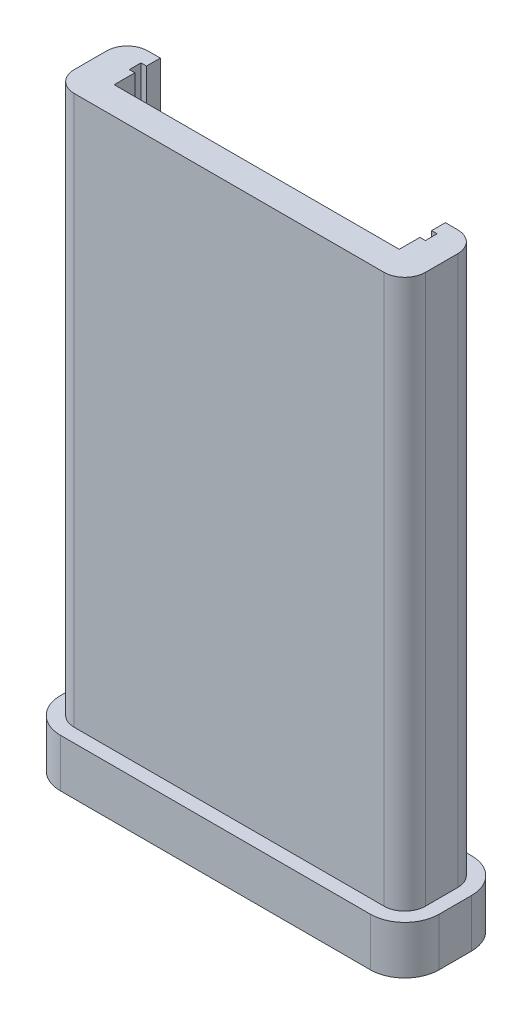
SolidWorks part; units mm, degrees
material "Melamine resin"
ref_plane "Front Plane" through (0, 0, 0) normal (0, 0, 1) x (1, 0, 0)
ref_plane "Top Plane" through (0, 0, 0) normal (0, 1, 0) x (1, 0, 0)
ref_plane "Right Plane" through (0, 0, 0) normal (1, 0, 0) x (0, 0, -1)
sketch "Sketch2" plane through (0, 0, 0) normal (0, 1, 0) x (1, 0, 0)
  line L1 (0, 0) -> (88.9, 0)
  line L2 (0, 0) -> (0, 152.4)
  line L3 (0, 152.4) -> (88.9, 152.4)
  line L10 (88.9, 152.4) -> (88.9, 0)
  dimension "D1" = 152.4
  dimension "D2" = 88.9
extrude "Boss-Extrude1" add sketch "Sketch2" along normal blind 5.9944 contours L3 L10 L1 L2
sketch "Sketch4" plane through (0, 5.9944, 0) normal (0, 1, 0) x (1, 0, 0)
  line L0 (0, 0) -> (0, 152.4) construction
  line L1 (0, 0) -> (88.9, 0) construction
  circle A0 centre (45.72, 109.8713) radius 2.7305
  circle A1 centre (45.72, 33.6713) radius 2.7305
  dimension "D3" = 5.461
  dimension "D4" = 5.461
  dimension "D1" = 76.2
  dimension "D2" = 45.72
  dimension "D5" = 33.6713
extrude "Cut-Extrude2" cut sketch "Sketch4" against normal through all both
sketch "Sketch5" plane through (0, 5.9944, 0) normal (0, 1, 0) x (1, 0, 0)
  line L0 (0, 152.4) -> (88.9, 152.4) construction
  line L1 (12.065, 16.129) -> (76.835, 16.129)
  line L2 (12.065, 16.129) -> (12.065, 2.54)
  line L3 (12.065, 2.54) -> (76.835, 2.54)
  line L4 (76.835, 16.129) -> (76.835, 2.54)
  line L5 (18.161, 7.62) -> (70.739, 7.62)
  line L6 (18.161, 7.62) -> (18.161, 16.129)
  line L7 (18.161, 16.129) -> (70.739, 16.129)
  line L8 (70.739, 7.62) -> (70.739, 16.129)
  line L9 (17.145, 13.589) -> (71.755, 13.589)
  line L10 (17.145, 13.589) -> (17.145, 11.43)
  line L11 (17.145, 11.43) -> (71.755, 11.43)
  line L12 (71.755, 13.589) -> (71.755, 11.43)
  line L13 (0, 0) -> (88.9, 0) construction
  point P16 (44.45, 152.4)
  point P17 (44.45, 16.129)
  dimension "D1" = 54.61
  dimension "D2" = 1.016
  dimension "D3" = 1.016
  dimension "D4" = 3.81
  dimension "D5" = 2.54
  dimension "D6" = 5.08
  dimension "D7" = 5.08
  dimension "D8" = 2.159
  dimension "D9" = 2.54
  dimension "D10" = 5.08
extrude "Boss-Extrude2" add sketch "Sketch5" along normal blind 101.6 contours L9 L12 L11 L8 L5 L6 L10 L1 L2 L3 L4
fillet "Fillet1" radius 3.81 4 edges at (12.065, 56.7944, -2.54) (12.065, 56.7944, -16.129) (76.835, 56.7944, -2.54) (76.835, 56.7944, -16.129)
sketch "Sketch7" plane through (0, 5.9944, 0) normal (0, 1, 0) x (1, 0, 0)
  line L0 (0, 0) -> (88.9, 0) construction
  line L1 (0, 152.4) -> (2.54, 152.4)
  line L2 (0, 152.4) -> (0, 0)
  line L3 (0, 0) -> (2.54, 0)
  line L4 (2.54, 152.4) -> (2.54, 0)
  dimension "D1" = 2.54
extrude "Cut-Extrude3" cut sketch "Sketch7" against normal through all both
sketch "Sketch11" plane through (0, 0, 0) normal (0, -1, 0) x (1, 0, 0)
  line L4 (2.54, 0) -> (2.54, -152.4)
  line L5 (2.54, -152.4) -> (88.9, -152.4)
  line L6 (88.9, -152.4) -> (88.9, 0)
  line L7 (88.9, 0) -> (2.54, 0)
  line L8 (2.54, 0) -> (2.54, -152.4)
  line L9 (2.54, -152.4) -> (88.9, -152.4)
  line L10 (88.9, -152.4) -> (88.9, 0)
  line L11 (88.9, 0) -> (2.54, 0)
  dimension "D1" = 0
extrude "Cut-Extrude4" cut sketch "Sketch11" against normal blind 6.35
sketch "Sketch12" plane through (0, 6.35, 0) normal (0, -1, 0) x (1, 0, 0)
  line L0 (18.161, -16.129) -> (70.739, -16.129)
  line L1 (70.739, -18.669) -> (73.025, -18.669)
  line L2 (79.375, -12.319) -> (79.375, -6.35)
  line L3 (73.025, 0) -> (15.875, 0)
  line L4 (9.525, -6.35) -> (9.525, -12.319)
  line L5 (15.875, -18.669) -> (18.161, -18.669)
  line L6 (18.161, -18.669) -> (70.739, -18.669)
  line L16 (71.755, -11.43) -> (71.755, -13.589)
  line L17 (71.755, -13.589) -> (70.739, -13.589)
  line L18 (70.739, -13.589) -> (70.739, -16.129)
  line L19 (70.739, -16.129) -> (73.025, -16.129)
  line L20 (76.835, -12.319) -> (76.835, -6.35)
  line L21 (73.025, -2.54) -> (15.875, -2.54)
  line L22 (12.065, -6.35) -> (12.065, -12.319)
  line L23 (15.875, -16.129) -> (18.161, -16.129)
  line L24 (18.161, -16.129) -> (18.161, -13.589)
  line L25 (18.161, -13.589) -> (17.145, -13.589)
  line L26 (17.145, -13.589) -> (17.145, -11.43)
  line L27 (17.145, -11.43) -> (18.161, -11.43)
  line L28 (18.161, -11.43) -> (18.161, -7.62)
  line L29 (18.161, -7.62) -> (70.739, -7.62)
  line L30 (70.739, -7.62) -> (70.739, -11.43)
  line L31 (70.739, -11.43) -> (71.755, -11.43)
  line L32 (71.755, -11.43) -> (71.755, -13.589)
  line L33 (71.755, -13.589) -> (70.739, -13.589)
  line L34 (70.739, -13.589) -> (70.739, -16.129)
  line L35 (70.739, -16.129) -> (73.025, -16.129)
  line L36 (76.835, -12.319) -> (76.835, -6.35)
  line L37 (73.025, -2.54) -> (15.875, -2.54)
  line L38 (12.065, -6.35) -> (12.065, -12.319)
  line L39 (15.875, -16.129) -> (18.161, -16.129)
  line L40 (18.161, -16.129) -> (18.161, -13.589)
  line L41 (18.161, -13.589) -> (17.145, -13.589)
  line L42 (17.145, -13.589) -> (17.145, -11.43)
  line L43 (17.145, -11.43) -> (18.161, -11.43)
  line L44 (18.161, -11.43) -> (18.161, -7.62)
  line L45 (18.161, -7.62) -> (70.739, -7.62)
  line L46 (70.739, -7.62) -> (70.739, -11.43)
  line L47 (70.739, -11.43) -> (71.755, -11.43)
  arc A0 (73.025, -18.669) -> (79.375, -12.319) centre (73.025, -12.319) ccw
  arc A1 (79.375, -6.35) -> (73.025, 0) centre (73.025, -6.35) ccw
  arc A2 (15.875, 0) -> (9.525, -6.35) centre (15.875, -6.35) ccw
  arc A3 (9.525, -12.319) -> (15.875, -18.669) centre (15.875, -12.319) ccw
  arc A4 (73.025, -16.129) -> (76.835, -12.319) centre (73.025, -12.319) ccw
  arc A5 (76.835, -6.35) -> (73.025, -2.54) centre (73.025, -6.35) ccw
  arc A6 (15.875, -2.54) -> (12.065, -6.35) centre (15.875, -6.35) ccw
  arc A7 (12.065, -12.319) -> (15.875, -16.129) centre (15.875, -12.319) ccw
  arc A8 (73.025, -16.129) -> (76.835, -12.319) centre (73.025, -12.319) ccw
  arc A9 (76.835, -6.35) -> (73.025, -2.54) centre (73.025, -6.35) ccw
  arc A10 (15.875, -2.54) -> (12.065, -6.35) centre (15.875, -6.35) ccw
  arc A11 (12.065, -12.319) -> (15.875, -16.129) centre (15.875, -12.319) ccw
  line M22 (71.755, -11.43) -> (71.755, -13.589)
  line M23 (71.755, -13.589) -> (70.739, -13.589)
  line M24 (70.739, -13.589) -> (70.739, -16.129)
  line M25 (70.739, -16.129) -> (73.025, -16.129)
  arc M26 (73.025, -16.129) -> (76.835, -12.319) centre (73.025, -12.319) ccw
  line M27 (76.835, -12.319) -> (76.835, -6.35)
  arc M28 (76.835, -6.35) -> (73.025, -2.54) centre (73.025, -6.35) ccw
  line M29 (73.025, -2.54) -> (15.875, -2.54)
  arc M30 (15.875, -2.54) -> (12.065, -6.35) centre (15.875, -6.35) ccw
  line M31 (12.065, -6.35) -> (12.065, -12.319)
  arc M32 (12.065, -12.319) -> (15.875, -16.129) centre (15.875, -12.319) ccw
  line M33 (15.875, -16.129) -> (18.161, -16.129)
  line M34 (18.161, -16.129) -> (18.161, -13.589)
  line M35 (18.161, -13.589) -> (17.145, -13.589)
  line M36 (17.145, -13.589) -> (17.145, -11.43)
  line M37 (17.145, -11.43) -> (18.161, -11.43)
  line M38 (18.161, -11.43) -> (18.161, -7.62)
  line M39 (18.161, -7.62) -> (70.739, -7.62)
  line M40 (70.739, -7.62) -> (70.739, -11.43)
  line M41 (70.739, -11.43) -> (71.755, -11.43)
  dimension "D1" = 0
  dimension "D2" = 2.54
extrude "Boss-Extrude3" add sketch "Sketch12" along normal blind 8.89 contours L4 A3 L5 L6 L1 A0 L2 A1 L3 A2 L0 M33 M32 M31 M30 M29 M28 M27 M26 M25 | M41 M22 M23 M24 M25 M26 M27 M28 M29 M30 M31 M32 M33 M34 M35 M36 M37 M38 M39 M40 | L0 M34 M24 M23 M22 M41 M40 M39 M38 M37 M36 M35
sketch "Sketch13" plane through (0, -2.54, 0) normal (0, -1, 0) x (1, 0, 0)
  line L0 (19.05, -9.3345) -> (69.85, -9.3345) construction
  line L1 (73.025, 0) -> (15.875, 0) construction
  line L2 (79.375, -12.319) -> (79.375, -6.35) construction
  circle A0 centre (19.05, -9.3345) radius 2.7305
  circle A1 centre (69.85, -9.3345) radius 2.7305
  point P6 (44.45, 0)
  point P7 (44.45, -9.3345)
  point P10 (79.375, -9.3345)
  dimension "D1" = 5.461
  dimension "D2" = 5.461
  dimension "D3" = 50.8
extrude "Cut-Extrude5" cut sketch "Sketch13" against normal blind 6.35
equation "\"threaded_insert_hole\"=0.1472"
equation "\"th\"=1.25249"
